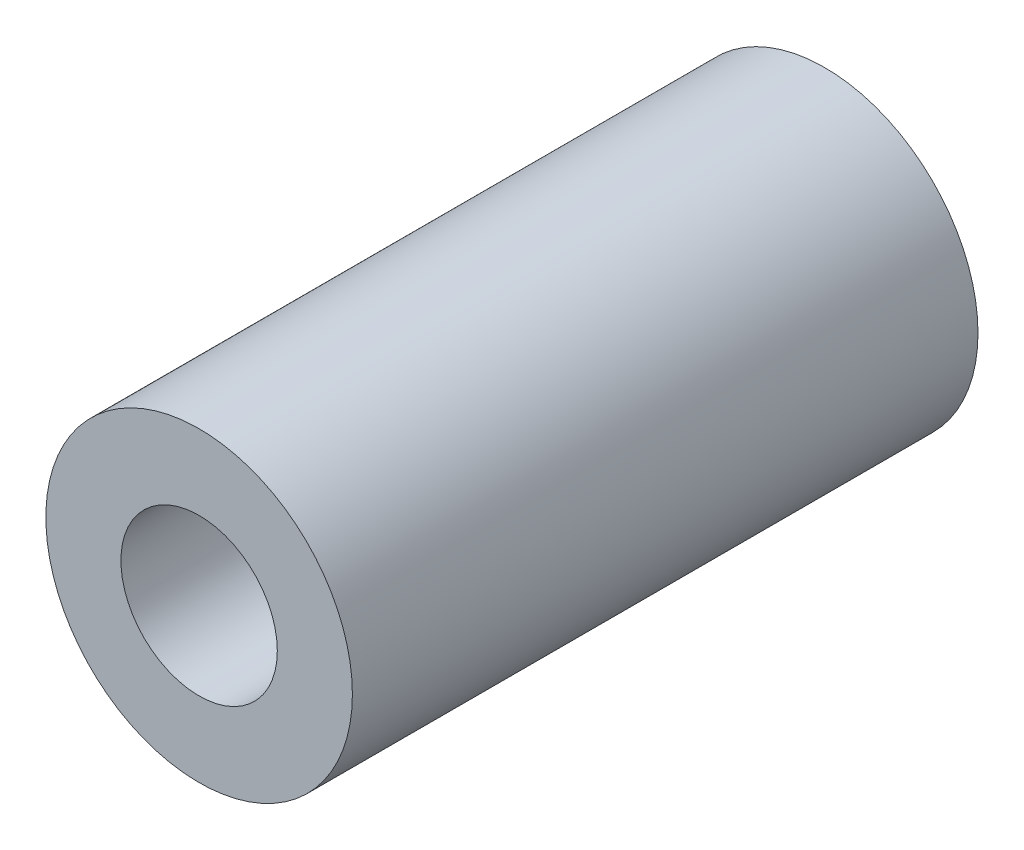
SolidWorks part; units mm, degrees
ref_plane "正面" through (0, 0, 0) normal (1, 0, 0) x (0, 1, 0)
ref_plane "平面" through (0, 0, 0) normal (0, 0, 1) x (0, 1, 0)
ref_plane "右側面" through (0, 0, 0) normal (0, 1, 0) x (-1, 0, 0)
sketch "ｽｹｯﾁ1" plane through (0, 0, 0) normal (0, 0, 1) x (0, 1, 0)
  circle A0 centre (0, 0) radius 2.45
  circle A1 centre (0, 0) radius 1.25
  dimension "D1" = 2.5
  dimension "D2" = 1.2
extrude "ﾎﾞｽ - 押し出し1" add sketch "ｽｹｯﾁ1" along normal blind 10
